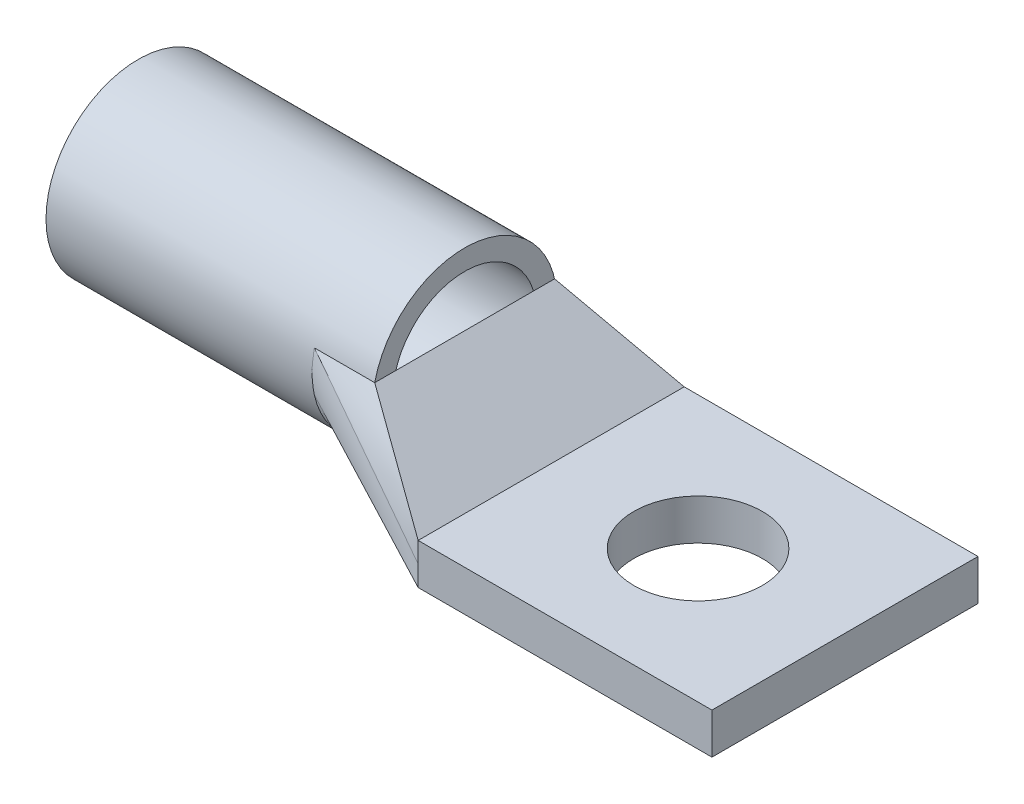
SolidWorks part; units mm, degrees
ref_plane "Front" through (0, 0, 0) normal (0, 0, 1) x (1, 0, 0)
ref_plane "Top" through (0, 0, 0) normal (0, 1, 0) x (1, 0, 0)
ref_plane "Right" through (0, 0, 0) normal (1, 0, 0) x (0, 0, -1)
sketch "Sketch1" plane through (0, 0, 0) normal (0, 1, 0) x (1, 0, 0)
  line L1 (11.43, 10.3505) -> (-11.43, 10.3505)
  line L2 (11.43, 10.3505) -> (11.43, -10.3505)
  line L3 (11.43, -10.3505) -> (-11.43, -10.3505)
  line L4 (-11.43, 10.3505) -> (-11.43, -10.3505)
  line L5 (0, -10.3505) -> (0, 10.3505) construction
  line L6 (11.43, 0) -> (-11.43, 0) construction
  circle A0 centre (0, 0) radius 5
  dimension "D1" = 10
  dimension "D3" = 22.86
  dimension "D2" = 20.701
extrude "Boss-Extrude1" add sketch "Sketch1" along normal blind 3.175
ref_plane "Plane1" through (-18.161, 0, 0) normal (-1, 0, 0) x (0, 0, 1)
ref_plane "Plane2" through (-43.561, 0, 0) normal (-1, 0, 0) x (0, 0, 1)
sketch "Sketch2" plane through (-43.561, 0, 0) normal (-1, 0, 0) x (0, 0, 1)
  circle A0 centre (0, 7.1755) radius 7.1755
  dimension "D1" = 14.351
extrude "Extrude-Thin1" add sketch "Sketch2" against normal up to surface (25.4 mm away) separate body thin contours A0 up to plane "Plane1" thin type one direction reverse wall 1.5875
ref_plane "Plane3" through (-22.86, 0, 0) normal (-1, 0, 0) x (0, 0, 1)
sketch3d "3DSketch4"
  line L2 (-22.86, 8.763, -6.9977) -> (-18.161, 8.763, -6.9977)
  line L3 (-22.86, 8.763, 6.9977) -> (-18.161, 8.763, 6.9977)
  line L5 (-18.161, 8.763, 6.9977) -> (-18.161, 8.763, -6.9977)
  line L7 (-22.86, 8.763, 6.9977) -> (-22.86, 5.588, 6.9977) construction
  line L8 (-22.86, 8.763, -6.9977) -> (-22.86, 5.588, -6.9977) construction
  circle A0 centre (-22.86, 7.1755, 0) radius 7.1755
  arc A1 (-22.86, 5.588, -6.9977) -> (-22.86, 5.588, 6.9977) centre (-22.86, 7.1755, 0) ccw
  circle A2 centre (-18.161, 7.1755, 0) radius 7.1755 construction
  arc A3 (-22.86, 5.588, 6.9977) -> (-22.86, 8.763, 6.9977) centre (-22.86, 7.1755, 0) cw
  arc A4 (-22.86, 8.763, -6.9977) -> (-22.86, 5.588, -6.9977) centre (-22.86, 7.1755, 0) cw
  point P2 (-30.0355, 7.1755, 0)
  point P4 (-30.0355, 7.1755, 0)
  point P13 (-10.9855, 7.1755, 0)
  point P14 (-30.0355, 7.1755, 0)
  point P15 (-30.0355, 7.1755, 0)
  dimension "D1" = 3.175
sketch "Sketch5" plane through (-11.43, 0, 0) normal (-1, 0, 0) x (0, 0, 1)
  line L0 (-10.3505, 3.175) -> (-10.3505, 1.5875)
  line L1 (-10.3505, 3.175) -> (-10.3505, 0) construction
  line L2 (-10.3505, 1.5875) -> (-10.3505, 0)
  line L3 (10.3505, 3.175) -> (10.3505, 1.5875)
  line L4 (-10.3505, 0) -> (10.3505, 0)
  line L5 (10.3505, 0) -> (10.3505, 3.175)
  line L6 (10.3505, 3.175) -> (-10.3505, 3.175)
  line L7 (-10.3505, 3.175) -> (-10.3505, 0)
  line L8 (-10.3505, 0) -> (10.3505, 0)
  line L10 (10.3505, 3.175) -> (-10.3505, 3.175)
  line L12 (10.3505, 3.175) -> (10.3505, 0) construction
  line L13 (10.3505, 1.5875) -> (10.3505, 0)
  dimension "D1" = 0
surface "Surface-Loft1"
sketch3d "3DSketch5"
  line L0 (-18.161, 7.1755, 0) -> (-43.561, 7.1755, 0)
  line L3 (0, 3.175, 0) -> (0, 0, 0)
  line L4 (0, 3.175, 0) -> (0, 0, 0) construction
  line L5 (-18.161, 7.1755, 0) -> (-43.561, 7.1755, 0) construction
